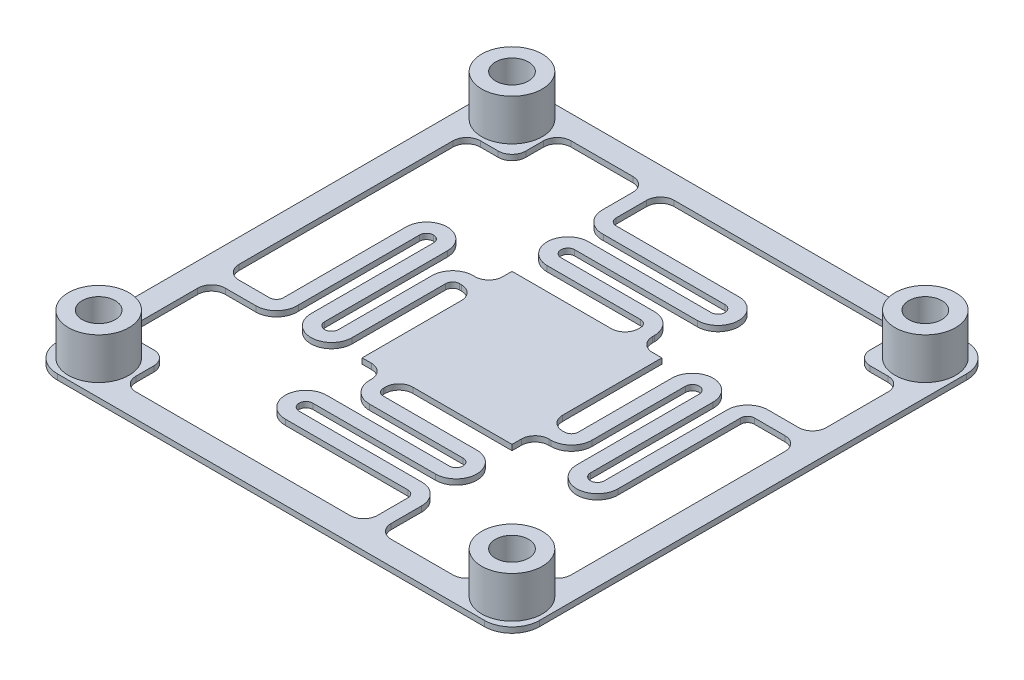
SolidWorks part; units mm, degrees
material "FR4"
ref_plane "Front Plane" through (0, 0, 0) normal (0, 0, 1) x (1, 0, 0)
ref_plane "Top Plane" through (0, 0, 0) normal (0, 1, 0) x (1, 0, 0)
ref_plane "Right Plane" through (0, 0, 0) normal (1, 0, 0) x (0, 0, -1)
sketch "Sketch1" plane through (0, 0, 0) normal (0, 1, 0) x (1, 0, 0)
  line L1 (-10.8947, 18.5234) -> (20.1053, 18.5234)
  line L2 (-12.8947, 16.5234) -> (-12.8947, -14.4766)
  line L3 (-10.8947, -16.4766) -> (20.1053, -16.4766)
  line L4 (22.1053, 16.5234) -> (22.1053, -14.4766)
  circle A0 centre (19.6053, 16.0234) radius 1.2
  circle A1 centre (-10.3947, 16.0234) radius 1.2
  circle A2 centre (-10.3947, -13.9766) radius 1.2
  circle A3 centre (19.6053, -13.9766) radius 1.2
  arc A4 (-12.8947, -14.4766) -> (-10.8947, -16.4766) centre (-10.8947, -14.4766) ccw
  arc A5 (20.1053, -16.4766) -> (22.1053, -14.4766) centre (20.1053, -14.4766) ccw
  arc A6 (22.1053, 16.5234) -> (20.1053, 18.5234) centre (20.1053, 16.5234) ccw
  arc A7 (-10.8947, 18.5234) -> (-12.8947, 16.5234) centre (-10.8947, 16.5234) ccw
  dimension "D11" = 35
  dimension "D12" = 2
  dimension "D2" = 35
  dimension "D3" = 32.5
  dimension "D4" = 30
  dimension "D5" = 30
  dimension "D6" = 30
  dimension "D7" = 32.5
  dimension "D8" = 32.5
  dimension "D9" = 32.5
  dimension "D10" = 32.5
extrude "Boss-Extrude1" add sketch "Sketch1" along normal blind 0.4
sketch "Sketch2" plane through (0, 0.4, 0) normal (0, 1, 0) x (1, 0, 0)
  circle A0 centre (19.6053, -13.9766) radius 1.2 construction
  circle A1 centre (19.6053, -13.9766) radius 1.2
  circle A2 centre (-10.3947, -13.9766) radius 1.2 construction
  circle A3 centre (-10.3947, -13.9766) radius 1.2
  circle A4 centre (-10.3947, 16.0234) radius 1.2 construction
  circle A5 centre (-10.3947, 16.0234) radius 1.2
  circle A6 centre (19.6053, 16.0234) radius 1.2 construction
  circle A7 centre (19.6053, 16.0234) radius 1.2
  circle A8 centre (-10.3947, -13.9766) radius 2.2
  circle A9 centre (-10.3947, 16.0234) radius 2.2
  circle A10 centre (19.6053, 16.0234) radius 2.2
  circle A11 centre (19.6053, -13.9766) radius 2.2
  dimension "D1" = 1
  dimension "D2" = 1
extrude "Boss-Extrude2" add sketch "Sketch2" along normal blind 3
sketch "Sketch3" plane through (0, 0, 0) normal (0, -1, 0) x (1, 0, 0)
  line L0 (-0.8336, -2.785) -> (-0.8336, 4.4155)
  line L1 (-1.9699, -3.785) -> (-1.8336, -3.785)
  line L2 (-2.4699, -3.285) -> (-2.4699, 3.4974)
  line L3 (-5.4699, 3.4974) -> (-5.4699, -5.4028)
  line L4 (4.6053, -1.0234) -> (4.6053, 16.4766) construction
  line L5 (-10.8947, 16.4766) -> (20.1053, 16.4766) construction
  line L6 (-6.4733, -5.4017) -> (-6.4733, 3.3973)
  line L7 (-7.9699, 4.9974) -> (-10.1834, 4.9974)
  line L8 (-1.9699, -4.785) -> (-1.8336, -4.785)
  line L9 (-3.4699, -3.285) -> (-3.4699, 3.4974)
  line L10 (-4.4699, 3.4974) -> (-4.4699, -5.4028)
  line L11 (-7.4699, -5.4028) -> (-7.4699, 3.4974)
  line L12 (-7.9699, 3.9974) -> (-10.1834, 3.9974)
  line L13 (-0.8336, -6.4622) -> (-0.8336, -5.785)
  line L14 (-7.8947, 12.4766) -> (-7.8947, 13.7652)
  line L15 (-10.1834, 11.4766) -> (-8.8947, 11.4766)
  line L16 (-11.1834, 5.9974) -> (-11.1834, 10.4766)
  line L17 (8.6261, 14.7652) -> (-6.8947, 14.7652)
  line L18 (-2.9699, -3.285) -> (-2.9699, 3.4974) construction
  line L19 (-4.9699, 3.4974) -> (-4.9699, -5.4028) construction
  line L20 (-6.9699, -5.4028) -> (-6.9699, 3.4974) construction
  line L21 (-7.9699, 4.4974) -> (-11.1834, 4.4974) construction
  line L22 (2.8436, 4.4155) -> (10.0441, 4.4155)
  line L23 (1.8436, 5.5518) -> (1.8436, 5.4155)
  line L24 (2.3436, 6.0518) -> (9.1261, 6.0518)
  line L25 (9.1261, 9.0518) -> (0.2259, 9.0518)
  line L26 (0.227, 10.0551) -> (9.026, 10.0551)
  line L27 (10.6261, 11.5518) -> (10.6261, 13.7652)
  line L28 (0.8436, 5.5518) -> (0.8436, 5.4155)
  line L29 (2.3436, 7.0518) -> (9.1261, 7.0518)
  line L30 (9.1261, 8.0518) -> (0.2259, 8.0518)
  line L31 (0.2259, 11.0518) -> (9.1261, 11.0518)
  line L32 (9.6261, 11.5518) -> (9.6261, 13.7652)
  line L33 (-0.8336, 4.4155) -> (-0.1564, 4.4155)
  line L34 (18.1053, 11.4766) -> (19.3939, 11.4766)
  line L35 (17.1053, 13.7652) -> (17.1053, 12.4766)
  line L36 (11.6261, 14.7652) -> (16.1053, 14.7652)
  line L37 (20.3939, -5.0442) -> (20.3939, 10.4766)
  line L38 (2.3436, 6.5518) -> (9.1261, 6.5518) construction
  line L39 (9.1261, 8.5518) -> (0.2259, 8.5518) construction
  line L40 (0.2259, 10.5518) -> (9.1261, 10.5518) construction
  line L41 (10.1261, 11.5518) -> (10.1261, 14.7652) construction
  line L42 (10.0441, 0.7382) -> (10.0441, -6.4622)
  line L43 (11.1805, 1.7382) -> (11.0441, 1.7382)
  line L44 (6.3669, -6.4622) -> (-0.8336, -6.4622)
  line L45 (11.6805, 1.2382) -> (11.6805, -5.5442)
  line L46 (7.3669, -7.5986) -> (7.3669, -7.4622)
  line L47 (6.8669, -8.0986) -> (0.0844, -8.0986)
  line L48 (14.6805, -5.5442) -> (14.6805, 3.356)
  line L49 (0.0844, -11.0986) -> (8.9846, -11.0986)
  line L50 (15.6838, 3.3549) -> (15.6838, -5.4441)
  line L51 (8.9835, -12.1019) -> (0.1845, -12.1019)
  line L52 (-1.4156, -13.5986) -> (-1.4156, -15.812)
  line L53 (8.3669, -7.5986) -> (8.3669, -7.4622)
  line L54 (6.8669, -9.0986) -> (0.0844, -9.0986)
  line L55 (17.1805, -7.0442) -> (19.3939, -7.0442)
  line L56 (0.0844, -10.0986) -> (8.9846, -10.0986)
  line L57 (11.1805, 2.7382) -> (11.0441, 2.7382)
  line L58 (8.9846, -13.0986) -> (0.0844, -13.0986)
  line L59 (-0.4156, -13.5986) -> (-0.4156, -15.812)
  line L60 (6.8669, -8.5986) -> (0.0844, -8.5986) construction
  line L61 (12.6805, 1.2382) -> (12.6805, -5.5442)
  line L62 (0.0844, -10.5986) -> (8.9846, -10.5986) construction
  line L63 (13.6805, -5.5442) -> (13.6805, 3.356)
  line L64 (8.9846, -12.5986) -> (0.0844, -12.5986) construction
  line L65 (-0.9156, -13.5986) -> (-0.9156, -16.812) construction
  line L66 (16.6805, 3.356) -> (16.6805, -5.5442)
  line L67 (17.1805, -6.0442) -> (19.3939, -6.0442)
  line L68 (10.0441, 4.4155) -> (10.0441, 3.7382)
  line L69 (17.1053, -14.5234) -> (17.1053, -15.812)
  line L70 (19.3939, -13.5234) -> (18.1053, -13.5234)
  line L71 (20.3939, -8.0442) -> (20.3939, -12.5234)
  line L72 (0.5844, -16.812) -> (16.1053, -16.812)
  line L73 (12.1805, 1.2382) -> (12.1805, -5.5442) construction
  line L74 (14.1805, -5.5442) -> (14.1805, 3.356) construction
  line L75 (16.1805, 3.356) -> (16.1805, -5.5442) construction
  line L76 (17.1805, -6.5442) -> (20.3939, -6.5442) construction
  line L92 (10.0441, -6.4622) -> (9.3669, -6.4622)
  line L101 (-8.8947, -13.5234) -> (-10.1834, -13.5234)
  line L102 (-7.8947, -15.812) -> (-7.8947, -14.5234)
  line L103 (-2.4156, -16.812) -> (-6.8947, -16.812)
  line L104 (-11.1834, 2.9974) -> (-11.1834, -12.5234)
  arc A0 (-2.4699, -3.285) -> (-1.9699, -3.785) centre (-1.9699, -3.285) ccw
  arc A1 (-3.9699, 4.9974) -> (-2.4699, 3.4974) centre (-3.9699, 3.4974) cw
  arc A2 (-5.4699, 3.4974) -> (-3.9699, 4.9974) centre (-3.9699, 3.4974) cw
  arc A3 (-5.9699, -5.9028) -> (-5.4699, -5.4028) centre (-5.9699, -5.4028) ccw
  arc A4 (-6.4733, -5.4017) -> (-5.9699, -5.9028) centre (-5.9722, -5.4017) ccw
  arc A5 (-6.4733, 3.3973) -> (-7.9699, 4.9974) centre (-7.9699, 3.4974) ccw
  arc A6 (-3.4699, -3.285) -> (-1.9699, -4.785) centre (-1.9699, -3.285) ccw
  arc A7 (-3.9699, 3.9974) -> (-3.4699, 3.4974) centre (-3.9699, 3.4974) cw
  arc A8 (-4.4699, 3.4974) -> (-3.9699, 3.9974) centre (-3.9699, 3.4974) cw
  arc A9 (-5.9699, -6.9028) -> (-4.4699, -5.4028) centre (-5.9699, -5.4028) ccw
  arc A10 (-7.4699, -5.4028) -> (-5.9699, -6.9028) centre (-5.9699, -5.4028) ccw
  arc A11 (-7.4699, 3.4974) -> (-7.9699, 3.9974) centre (-7.9699, 3.4974) ccw
  arc A12 (-11.1834, 10.4766) -> (-10.1834, 11.4766) centre (-10.1834, 10.4766) cw
  arc A13 (-8.8947, 11.4766) -> (-7.8947, 12.4766) centre (-8.8947, 12.4766) ccw
  arc A14 (-7.8947, 13.7652) -> (-6.8947, 14.7652) centre (-6.8947, 13.7652) cw
  arc A15 (-1.8336, -4.785) -> (-0.8336, -5.785) centre (-1.8336, -5.785) cw
  arc A16 (-1.8336, -3.785) -> (-0.8336, -2.785) centre (-1.8336, -2.785) ccw
  arc A17 (-10.1834, 4.9974) -> (-11.1834, 5.9974) centre (-10.1834, 5.9974) cw
  arc A18 (-10.1834, 3.9974) -> (-11.1834, 2.9974) centre (-10.1834, 2.9974) ccw
  arc A19 (-6.9699, -5.4028) -> (-5.9699, -6.4028) centre (-5.9699, -5.4028) ccw construction
  arc A20 (-5.9699, -6.4028) -> (-4.9699, -5.4028) centre (-5.9699, -5.4028) ccw construction
  arc A21 (-4.9699, 3.4974) -> (-3.9699, 4.4974) centre (-3.9699, 3.4974) cw construction
  arc A22 (-3.9699, 4.4974) -> (-2.9699, 3.4974) centre (-3.9699, 3.4974) cw construction
  arc A23 (-6.9699, 3.4974) -> (-7.9699, 4.4974) centre (-7.9699, 3.4974) ccw construction
  arc A24 (-2.9699, -3.285) -> (-1.9699, -4.285) centre (-1.9699, -3.285) ccw construction
  arc A25 (2.3436, 6.0518) -> (1.8436, 5.5518) centre (2.3436, 5.5518) ccw
  arc A26 (10.6261, 7.5518) -> (9.1261, 6.0518) centre (9.1261, 7.5518) cw
  arc A27 (9.1261, 9.0518) -> (10.6261, 7.5518) centre (9.1261, 7.5518) cw
  arc A28 (-0.2741, 9.5518) -> (0.2259, 9.0518) centre (0.2259, 9.5518) ccw
  arc A29 (0.227, 10.0551) -> (-0.2741, 9.5518) centre (0.227, 9.554) ccw
  arc A30 (9.026, 10.0551) -> (10.6261, 11.5518) centre (9.1261, 11.5518) ccw
  arc A31 (2.3436, 7.0518) -> (0.8436, 5.5518) centre (2.3436, 5.5518) ccw
  arc A32 (9.6261, 7.5518) -> (9.1261, 7.0518) centre (9.1261, 7.5518) cw
  arc A33 (9.1261, 8.0518) -> (9.6261, 7.5518) centre (9.1261, 7.5518) cw
  arc A34 (-1.2741, 9.5518) -> (0.2259, 8.0518) centre (0.2259, 9.5518) ccw
  arc A35 (0.2259, 11.0518) -> (-1.2741, 9.5518) centre (0.2259, 9.5518) ccw
  arc A36 (6.8669, -8.0986) -> (7.3669, -7.5986) centre (6.8669, -7.5986) ccw
  arc A37 (-1.4156, -9.5986) -> (0.0844, -8.0986) centre (0.0844, -9.5986) cw
  arc A38 (0.0844, -11.0986) -> (-1.4156, -9.5986) centre (0.0844, -9.5986) cw
  arc A39 (9.4846, -11.5986) -> (8.9846, -11.0986) centre (8.9846, -11.5986) ccw
  arc A40 (8.9835, -12.1019) -> (9.4846, -11.5986) centre (8.9835, -11.6008) ccw
  arc A41 (0.1845, -12.1019) -> (-1.4156, -13.5986) centre (0.0844, -13.5986) ccw
  arc A42 (6.8669, -9.0986) -> (8.3669, -7.5986) centre (6.8669, -7.5986) ccw
  arc A43 (-0.4156, -9.5986) -> (0.0844, -9.0986) centre (0.0844, -9.5986) cw
  arc A44 (0.0844, -10.0986) -> (-0.4156, -9.5986) centre (0.0844, -9.5986) cw
  arc A45 (10.4846, -11.5986) -> (8.9846, -10.0986) centre (8.9846, -11.5986) ccw
  arc A46 (8.9846, -13.0986) -> (10.4846, -11.5986) centre (8.9846, -11.5986) ccw
  arc A47 (0.0844, -13.0986) -> (-0.4156, -13.5986) centre (0.0844, -13.5986) ccw
  arc A48 (8.9846, -12.5986) -> (9.9846, -11.5986) centre (8.9846, -11.5986) ccw construction
  arc A49 (9.9846, -11.5986) -> (8.9846, -10.5986) centre (8.9846, -11.5986) ccw construction
  arc A50 (0.0844, -10.5986) -> (-0.9156, -9.5986) centre (0.0844, -9.5986) cw construction
  arc A51 (-0.9156, -9.5986) -> (0.0844, -8.5986) centre (0.0844, -9.5986) cw construction
  arc A52 (0.0844, -12.5986) -> (-0.9156, -13.5986) centre (0.0844, -13.5986) ccw construction
  arc A53 (6.8669, -8.5986) -> (7.8669, -7.5986) centre (6.8669, -7.5986) ccw construction
  arc A54 (9.1261, 11.0518) -> (9.6261, 11.5518) centre (9.1261, 11.5518) ccw
  arc A55 (16.1053, 14.7652) -> (17.1053, 13.7652) centre (16.1053, 13.7652) cw
  arc A56 (17.1053, 12.4766) -> (18.1053, 11.4766) centre (18.1053, 12.4766) ccw
  arc A57 (19.3939, 11.4766) -> (20.3939, 10.4766) centre (19.3939, 10.4766) cw
  arc A58 (0.8436, 5.4155) -> (-0.1564, 4.4155) centre (-0.1564, 5.4155) cw
  arc A59 (1.8436, 5.4155) -> (2.8436, 4.4155) centre (2.8436, 5.4155) ccw
  arc A60 (10.6261, 13.7652) -> (11.6261, 14.7652) centre (11.6261, 13.7652) cw
  arc A61 (9.6261, 13.7652) -> (8.6261, 14.7652) centre (8.6261, 13.7652) ccw
  arc A62 (0.2259, 10.5518) -> (-0.7741, 9.5518) centre (0.2259, 9.5518) ccw construction
  arc A63 (-0.7741, 9.5518) -> (0.2259, 8.5518) centre (0.2259, 9.5518) ccw construction
  arc A64 (9.1261, 8.5518) -> (10.1261, 7.5518) centre (9.1261, 7.5518) cw construction
  arc A65 (10.1261, 7.5518) -> (9.1261, 6.5518) centre (9.1261, 7.5518) cw construction
  arc A66 (9.1261, 10.5518) -> (10.1261, 11.5518) centre (9.1261, 11.5518) ccw construction
  arc A67 (2.3436, 6.5518) -> (1.3436, 5.5518) centre (2.3436, 5.5518) ccw construction
  arc A68 (11.6805, 1.2382) -> (11.1805, 1.7382) centre (11.1805, 1.2382) ccw
  arc A69 (13.1805, -7.0442) -> (11.6805, -5.5442) centre (13.1805, -5.5442) cw
  arc A70 (14.6805, -5.5442) -> (13.1805, -7.0442) centre (13.1805, -5.5442) cw
  arc A71 (15.1805, 3.856) -> (14.6805, 3.356) centre (15.1805, 3.356) ccw
  arc A72 (15.6838, 3.3549) -> (15.1805, 3.856) centre (15.1827, 3.3549) ccw
  arc A73 (15.6838, -5.4441) -> (17.1805, -7.0442) centre (17.1805, -5.5442) ccw
  arc A74 (12.6805, 1.2382) -> (11.1805, 2.7382) centre (11.1805, 1.2382) ccw
  arc A75 (13.1805, -6.0442) -> (12.6805, -5.5442) centre (13.1805, -5.5442) cw
  arc A76 (13.6805, -5.5442) -> (13.1805, -6.0442) centre (13.1805, -5.5442) cw
  arc A77 (15.1805, 4.856) -> (13.6805, 3.356) centre (15.1805, 3.356) ccw
  arc A78 (-6.8947, -16.812) -> (-7.8947, -15.812) centre (-6.8947, -15.812) cw
  arc A79 (-7.8947, -14.5234) -> (-8.8947, -13.5234) centre (-8.8947, -14.5234) ccw
  arc A80 (-10.1834, -13.5234) -> (-11.1834, -12.5234) centre (-10.1834, -12.5234) cw
  arc A81 (16.6805, 3.356) -> (15.1805, 4.856) centre (15.1805, 3.356) ccw
  arc A82 (16.6805, -5.5442) -> (17.1805, -6.0442) centre (17.1805, -5.5442) ccw
  arc A83 (20.3939, -12.5234) -> (19.3939, -13.5234) centre (19.3939, -12.5234) cw
  arc A84 (8.3669, -7.4622) -> (9.3669, -6.4622) centre (9.3669, -7.4622) cw
  arc A85 (7.3669, -7.4622) -> (6.3669, -6.4622) centre (6.3669, -7.4622) ccw
  arc A86 (18.1053, -13.5234) -> (17.1053, -14.5234) centre (18.1053, -14.5234) ccw
  arc A87 (17.1053, -15.812) -> (16.1053, -16.812) centre (16.1053, -15.812) cw
  arc A88 (11.0441, 2.7382) -> (10.0441, 3.7382) centre (11.0441, 3.7382) cw
  arc A89 (11.0441, 1.7382) -> (10.0441, 0.7382) centre (11.0441, 0.7382) ccw
  arc A90 (19.3939, -7.0442) -> (20.3939, -8.0442) centre (19.3939, -8.0442) cw
  arc A91 (19.3939, -6.0442) -> (20.3939, -5.0442) centre (19.3939, -5.0442) ccw
  arc A92 (16.1805, 3.356) -> (15.1805, 4.356) centre (15.1805, 3.356) ccw construction
  arc A93 (15.1805, 4.356) -> (14.1805, 3.356) centre (15.1805, 3.356) ccw construction
  arc A94 (-1.4156, -15.812) -> (-2.4156, -16.812) centre (-2.4156, -15.812) cw
  arc A95 (-0.4156, -15.812) -> (0.5844, -16.812) centre (0.5844, -15.812) ccw
  arc A96 (14.1805, -5.5442) -> (13.1805, -6.5442) centre (13.1805, -5.5442) cw construction
  arc A97 (13.1805, -6.5442) -> (12.1805, -5.5442) centre (13.1805, -5.5442) cw construction
  arc A98 (16.1805, -5.5442) -> (17.1805, -6.5442) centre (17.1805, -5.5442) ccw construction
  arc A99 (12.1805, 1.2382) -> (11.1805, 2.2382) centre (11.1805, 1.2382) ccw construction
  point P308 (4.6053, -1.0234)
extrude "Cut-Extrude1" cut sketch "Sketch3" against normal blind 3
